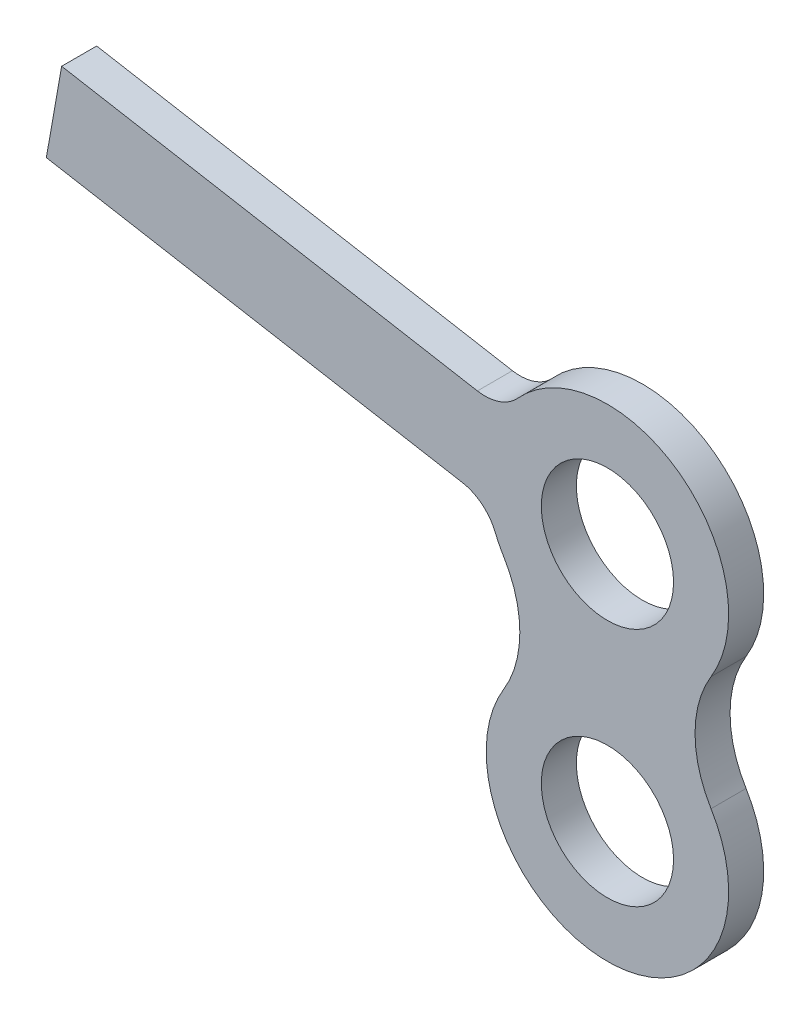
SolidWorks part; units mm, degrees
ref_plane "Front Plane" through (0, 0, 0) normal (0, 0, 1) x (1, 0, 0)
ref_plane "Top Plane" through (0, 0, 0) normal (0, 1, 0) x (1, 0, 0)
ref_plane "Right Plane" through (0, 0, 0) normal (1, 0, 0) x (0, 0, -1)
sketch "Sketch1" plane through (0, 0, 0) normal (0, 0, 1) x (1, 0, 0)
  line L0 (0, 10.9) -> (-25.1126, 15.328) construction
  line L1 (0, 10.9) -> (0, 0) construction
  line L4 (-24.7653, 17.2976) -> (-25.4599, 13.3584)
  line L5 (-5.9006, 13.9713) -> (-24.7653, 17.2976)
  line L7 (-6.5952, 10.0321) -> (-25.4599, 13.3584)
  arc A0 (-5.0912, 8.8191) -> (-4.7011, 8.0452) centre (0, 10.9) ccw
  circle A1 centre (0, 10.9) radius 3
  arc A2 (-4.7011, 2.8548) -> (4.7011, 2.8548) centre (0, 0) ccw
  circle A3 centre (0, 0) radius 3
  arc A4 (4.7011, 8.0452) -> (-4.0724, 14.5967) centre (0, 10.9) ccw
  arc A5 (-4.7011, 2.8548) -> (-4.7011, 8.0452) centre (-8.9748, 5.45) ccw
  arc A6 (4.7011, 2.8548) -> (4.7011, 8.0452) centre (8.9748, 5.45) cw
  arc A7 (-5.0912, 8.8191) -> (-6.5952, 10.0321) centre (-6.9425, 8.0624) ccw
  arc A8 (-5.9006, 13.9713) -> (-4.0724, 14.5967) centre (-5.5533, 15.9409) ccw
  dimension "D1" = 5
  dimension "D2" = 5
  dimension "D3" = 10.9
  dimension "D4" = 100
  dimension "D5" = 2
  dimension "D6" = 2
  dimension "D7" = 25.5
  dimension "D8" = 5.5
  dimension "D9" = 2
  dimension "D10" = 2
extrude "Boss-Extrude1" add sketch "Sketch1" along normal blind 1.59 contours A8 L5 L4 L7 A7 A0 A5 A2 A6 A4 A3 A1
